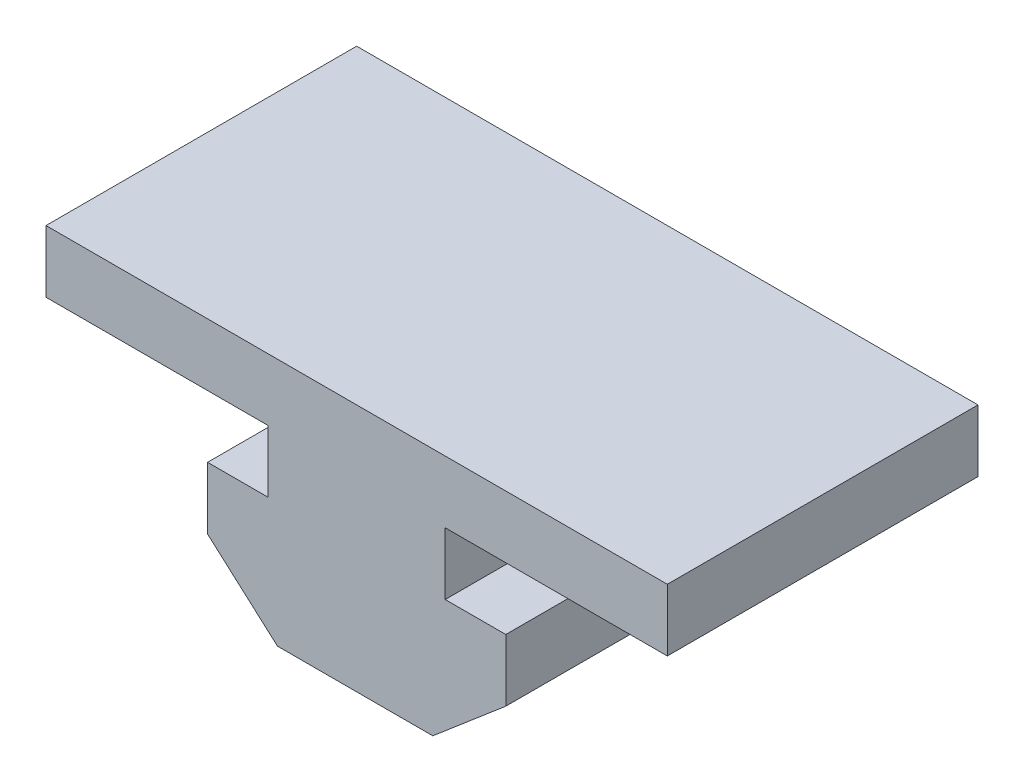
SolidWorks part; units mm, degrees
ref_plane "Front Plane" through (0, 0, 0) normal (0, 0, 1) x (1, 0, 0)
ref_plane "Top Plane" through (0, 0, 0) normal (0, 1, 0) x (1, 0, 0)
ref_plane "Right Plane" through (0, 0, 0) normal (1, 0, 0) x (0, 0, -1)
sketch "Sketch2" plane through (0, 0, 0) normal (0, 0, 1) x (1, 0, 0)
  line L1 (-2.5, -1.65) -> (2.5, -1.65)
  line L5 (-4.75, 2.35) -> (-2.8, 2.35)
  line L6 (2.9, 2.35) -> (4.85, 2.35)
  line L8 (-4.75, 2.35) -> (-4.75, 0.35)
  line L9 (-4.75, 0.35) -> (-2.5, -1.65)
  line L10 (4.85, 2.35) -> (4.85, 0.35)
  line L11 (4.85, 0.35) -> (2.5, -1.65)
  line L12 (-2.8, 4.35) -> (-9.95, 4.35)
  line L13 (-2.8, 2.35) -> (-2.8, 4.448) construction
  line L14 (-2.8, 2.35) -> (-2.8, 4.35)
  line L15 (2.9, 4.35) -> (10.05, 4.35)
  line L16 (-9.95, 4.35) -> (-9.95, 6.35)
  line L17 (2.9, 2.35) -> (2.9, 4.35)
  line L21 (10.05, 4.35) -> (10.05, 6.35)
  line L22 (-9.95, 6.35) -> (10.05, 6.35)
  point P0 (0, 0)
  dimension "D1" = 2
  dimension "D2" = 2
  dimension "D3" = 2
  dimension "D5" = 2
extrude "Boss-Extrude1" add sketch "Sketch2" along normal blind 10
